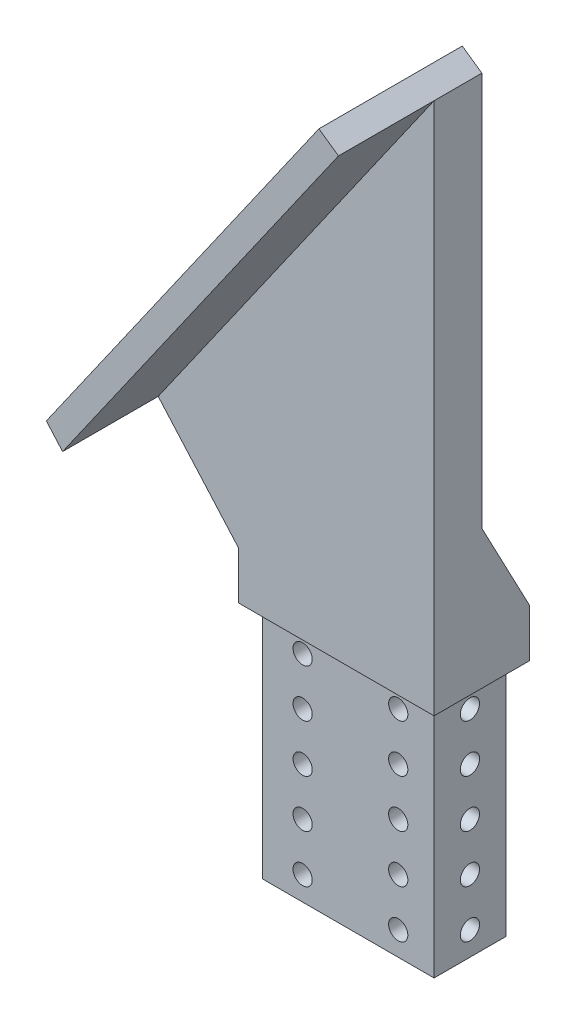
SolidWorks part; units mm, degrees
material "6061-T6 (SS)"
ref_plane "Front Plane" through (0, 0, 0) normal (0, 0, 1) x (1, 0, 0)
ref_plane "Top Plane" through (0, 0, 0) normal (0, 1, 0) x (1, 0, 0)
ref_plane "Right Plane" through (0, 0, 0) normal (1, 0, 0) x (0, 0, -1)
sketch "Sketch1" plane through (0, 0, 0) normal (0, 0, 1) x (1, 0, 0)
  line L0 (0, 0) -> (0, 76.2)
  line L1 (0, 76.2) -> (-101, 76.2)
  line L2 (-101, 76.2) -> (-101, 254)
  line L3 (-101, 254) -> (153, 254)
  line L4 (153, 254) -> (153, 76.2)
  line L5 (153, 76.2) -> (52, 76.2)
  line L6 (52, 76.2) -> (52, 0)
  line L7 (52, 0) -> (0, 0)
  point P3 (26, 254)
  dimension "D1" = 254
  dimension "D2" = 177.8
  dimension "D3" = 76.2
extrude "Boss-Extrude1" add sketch "Sketch1" along normal blind 25.4
sketch "Sketch2" plane through (0, 0, 25.4) normal (0, 0, 1) x (1, 0, 0)
  line L0 (52, 0) -> (52, 76.2) construction
  line L1 (0, 0) -> (52, 0)
  line L2 (0, 0) -> (0, 63.5)
  line L3 (0, 63.5) -> (52, 63.5)
  line L4 (52, 0) -> (52, 63.5)
  dimension "D1" = 63.5
sketch "Sketch3" plane through (0, 0, 0) normal (-1, 0, 0) x (0, 0, 1)
  line L0 (25.4, 0) -> (25.4, 63.5) construction
  line L1 (25.4, 63.5) -> (0, 63.5)
  line L2 (25.4, 63.5) -> (25.4, 0)
  line L3 (25.4, 0) -> (0, 0)
  line L4 (0, 63.5) -> (0, 0)
sketch "Sketch4" plane through (0, 0, 0) normal (0, 0, -1) x (-1, 0, 0)
  line L1 (0, 63.5) -> (-52, 63.5)
  line L2 (0, 63.5) -> (0, 0)
  line L3 (0, 0) -> (-52, 0)
  line L4 (-52, 63.5) -> (-52, 0)
sketch "Sketch5" plane through (52, 0, 0) normal (1, 0, 0) x (0, 0, -1)
  line L1 (0, 63.5) -> (-25.4, 63.5)
  line L2 (0, 63.5) -> (0, 0)
  line L3 (0, 0) -> (-25.4, 0)
  line L4 (-25.4, 63.5) -> (-25.4, 0)
extrude "Cut-Extrude1" cut sketch "Sketch2" against normal blind 3.175
extrude "Cut-Extrude2" cut sketch "Sketch3" against normal blind 3.175
extrude "Cut-Extrude3" cut sketch "Sketch4" against normal blind 3.175
extrude "Cut-Extrude4" cut sketch "Sketch5" against normal blind 3.175
sketch "Sketch6" plane through (0, 0, 3.175) normal (0, 0, -1) x (-1, 0, 0)
  line L0 (-48.825, 63.5) -> (-48.825, 0) construction
  line L1 (-3.175, 63.5) -> (-48.825, 63.5) construction
  line L2 (-48.825, 0) -> (-3.175, 0) construction
  circle A0 centre (-39.3, 57.15) radius 2.5527
  circle A1 centre (-13.9, 57.15) radius 2.5527
  circle A2 centre (-39.3, 44.45) radius 2.5527
  circle A3 centre (-13.9, 44.45) radius 2.5527
  circle A4 centre (-39.3, 31.75) radius 2.5527
  circle A5 centre (-13.9, 31.75) radius 2.5527
  circle A6 centre (-39.3, 19.05) radius 2.5527
  circle A7 centre (-13.9, 19.05) radius 2.5527
  circle A8 centre (-39.3, 6.35) radius 2.5527
  circle A9 centre (-13.9, 6.35) radius 2.5527
  dimension "D1" = 25.4
  dimension "D2" = 9.525
  dimension "D3" = 5.1054
  dimension "D4" = 5.1054
  dimension "D5" = 6.35
  dimension "D7" = 12.7
  dimension "D8" = 6.35
  dimension "D6" = 5
sketch "Sketch7" plane through (48.825, 0, 0) normal (1, 0, 0) x (0, 0, -1)
  line L0 (0, 63.5) -> (-25.4, 63.5) construction
  line L1 (-22.225, 0) -> (-22.225, 63.5) construction
  circle A0 centre (-12.7, 57.15) radius 2.5527
  circle A1 centre (-12.7, 44.45) radius 2.5527
  circle A2 centre (-12.7, 31.75) radius 2.5527
  circle A3 centre (-12.7, 19.05) radius 2.5527
  circle A4 centre (-12.7, 6.35) radius 2.5527
  dimension "D1" = 5.1054
  dimension "D2" = 6.35
  dimension "D3" = 9.525
  dimension "D5" = 12.7
  dimension "D4" = 5
extrude "Cut-Extrude5" cut sketch "Sketch6" against normal through all
extrude "Cut-Extrude6" cut sketch "Sketch7" against normal through all
sketch "Sketch8" plane through (0, 0, 25.4) normal (0, 0, 1) x (1, 0, 0)
  line L1 (52, 76.2) -> (153, 76.2)
  line L2 (52, 76.2) -> (52, 254)
  line L3 (52, 254) -> (153, 254)
  line L4 (153, 76.2) -> (153, 254)
extrude "Cut-Extrude7" cut sketch "Sketch8" against normal through all
sketch "Sketch9" plane through (0, 0, 25.4) normal (0, 0, 1) x (1, 0, 0)
  line L0 (52, 254) -> (52, 242.697)
  line L1 (52, 63.5) -> (52, 254) construction
  line L2 (52, 242.697) -> (35.8576, 254)
  line L3 (52, 254) -> (-101, 254) construction
  line L4 (35.8576, 254) -> (52, 254)
  dimension "D1" = 35
  dimension "D2" = 11.303
extrude "Cut-Extrude8" cut sketch "Sketch9" against normal through all and the other way through all
sketch "Sketch10" plane through (0, 0, 25.4) normal (0, 0, 1) x (1, 0, 0)
  line L0 (35.8576, 254) -> (-101, 58.547)
  line L1 (-101, 58.547) -> (-101, 254)
  line L2 (-101, 254) -> (35.8576, 254)
  dimension "D1" = 55
extrude "Cut-Extrude9" cut sketch "Sketch10" against normal through all
sketch "Sketch11" plane through (0, 0, 25.4) normal (0, 0, 1) x (1, 0, 0)
  line L0 (35.8576, 254) -> (46.7977, 246.3397)
  line L1 (52, 242.697) -> (35.8576, 254) construction
  line L2 (46.7977, 246.3397) -> (-82.8298, 61.2124)
  line L3 (-82.8298, 61.2124) -> (-93.7699, 68.8727)
  line L4 (-93.7699, 68.8727) -> (35.8576, 254)
  dimension "D1" = 13.3553
  dimension "D2" = 13.3553
  dimension "D3" = 225.9987
extrude "Cut-Extrude10" cut sketch "Sketch11" against normal through all
sketch "Sketch14" plane through (0, 0, 25.4) normal (0, 0, 1) x (1, 0, 0)
  line L1 (46.7977, 246.3397) -> (69.6855, 230.3135)
  line L2 (69.6855, 230.3135) -> (-62.703, 41.2431)
  line L3 (-62.703, 41.2431) -> (-85.5908, 57.2693)
  line L4 (-85.5908, 57.2693) -> (46.7977, 246.3397)
  dimension "D1" = 27.9409
extrude "Boss-Extrude2" add sketch "Sketch14" along normal blind 25.4
sketch "Sketch15" plane through (0, 0, 50.8) normal (0, 0, 1) x (1, 0, 0)
  line L0 (-38.2259, 76.2) -> (-72.3354, 76.2)
  line L1 (-72.3354, 76.2) -> (-85.5908, 57.2693)
  line L2 (-85.5908, 57.2693) -> (-62.703, 41.2431)
  line L3 (-62.703, 41.2431) -> (-38.2259, 76.2)
extrude "Cut-Extrude11" cut sketch "Sketch15" against normal through all
sketch "Sketch16" plane through (0, 0, 0) normal (0, 0, -1) x (-1, 0, 0)
  line L0 (0, 76.2) -> (40.323, 121.9184)
  line L1 (72.3354, 76.2) -> (-46.7977, 246.3397) construction
  line L2 (40.323, 121.9184) -> (72.3354, 76.2)
  line L3 (72.3354, 76.2) -> (0, 76.2)
  dimension "D1" = 60.96
extrude "Cut-Extrude12" cut sketch "Sketch16" against normal through all
sketch "Sketch17" plane through (52, 0, 0) normal (1, 0, 0) x (0, 0, -1)
  line L0 (-12.7, 246.3397) -> (-12.7, 100.2897)
  line L1 (0, 246.3397) -> (-50.8, 246.3397) construction
  line L2 (-12.7, 100.2897) -> (0, 76.2)
  line L3 (0, 63.5) -> (0, 242.697) construction
  line L4 (0, 76.2) -> (0, 246.3397)
  line L5 (0, 246.3397) -> (-12.7, 246.3397)
  dimension "D1" = 12.7
  dimension "D2" = 146.05
  dimension "D3" = 12.7
extrude "Cut-Extrude13" cut sketch "Sketch17" against normal through all
sketch "Sketch18" plane through (0, 0, 50.8) normal (0, 0, 1) x (1, 0, 0)
  line L0 (64.4832, 233.9562) -> (-27.012, 103.2875)
  line L1 (69.6855, 230.3135) -> (46.7977, 246.3397) construction
  line L2 (-23.8898, 100.2897) -> (-27.012, 103.2875) construction
  line L3 (-27.012, 103.2875) -> (-44.6975, 115.671)
  line L4 (-44.6975, 115.671) -> (46.7977, 246.3397)
  line L5 (46.7977, 246.3397) -> (64.4832, 233.9562)
  dimension "D1" = 21.59
  dimension "D2" = 21.59
extrude "Cut-Extrude14" cut sketch "Sketch18" against normal through all
sketch "Sketch19" plane through (0, 0, 25.4) normal (0, 0, -1) x (-1, 0, 0)
  line L0 (-52, 205.056) -> (-52, 216.1284)
  line L1 (-52, 216.1284) -> (-64.4832, 233.9562)
  line L2 (-64.4832, 233.9562) -> (-69.6855, 230.3135)
  line L3 (-69.6855, 230.3135) -> (-52, 205.056)
extrude "Cut-Extrude15" cut sketch "Sketch19" against normal through all
sketch "Sketch20" plane through (0, 0, 50.8) normal (0, 0, 1) x (1, 0, 0)
  line L0 (52, 205.056) -> (46.7977, 208.6987)
  line L1 (-25.6307, 105.2602) -> (52, 216.1284) construction
  line L2 (46.7977, 208.6987) -> (52, 216.1284)
  line L3 (52, 205.056) -> (52, 216.1284) construction
  line L4 (52, 216.1284) -> (52, 205.056)
extrude "Cut-Extrude16" cut sketch "Sketch20" against normal through all
